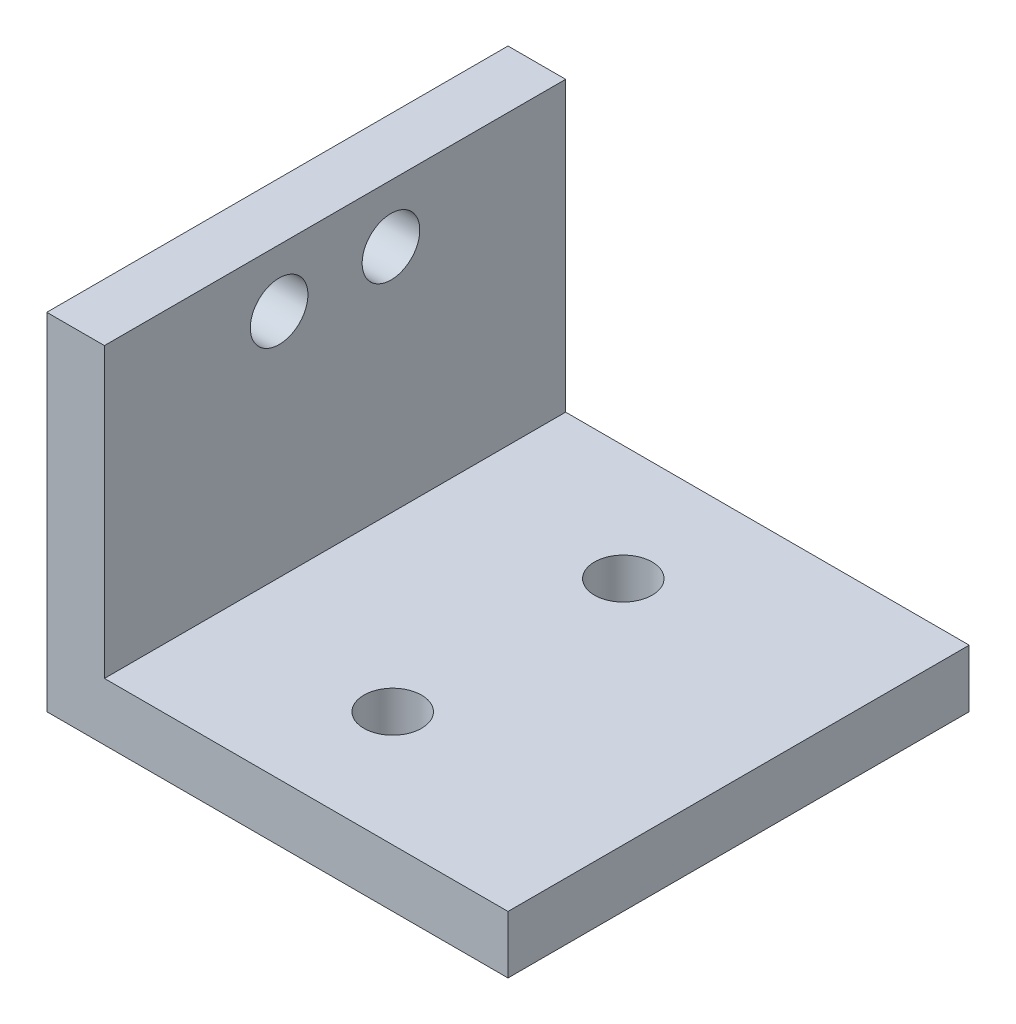
SolidWorks part; units mm, degrees
material "1060 Alloy"
ref_plane "Front Plane" through (0, 0, 0) normal (0, 0, 1) x (1, 0, 0)
ref_plane "Top Plane" through (0, 0, 0) normal (0, 1, 0) x (1, 0, 0)
ref_plane "Right Plane" through (0, 0, 0) normal (1, 0, 0) x (0, 0, -1)
sketch "Sketch1" plane through (0, 0, 0) normal (0, 0, 1) x (1, 0, 0)
  line L0 (0, 0) -> (0, 30)
  line L1 (0, 0) -> (40, 0)
  line L2 (5, 5) -> (40, 5)
  line L3 (5, 5) -> (5, 30)
  line L4 (5, 30) -> (0, 30)
  line L5 (40, 5) -> (40, 0)
  dimension "D1" = 5
extrude "Boss-Extrude1" add sketch "Sketch1" along normal blind 40
sketch "Sketch2" plane through (0, 0, 0) normal (-1, 0, 0) x (0, 0, 1)
  line L0 (40, 0) -> (0, 0) construction
  line L2 (40, 30) -> (40, 0) construction
  circle A0 centre (24.85, 25) radius 2.5
  circle A1 centre (15.15, 25) radius 2.5
  dimension "D1" = 9.7
  dimension "D2" = 25
  dimension "D3" = 15.15
extrude "Cut-Extrude1" cut sketch "Sketch2" against normal blind 40
sketch "Sketch3" plane through (0, 0, 0) normal (0, -1, 0) x (1, 0, 0)
  line L0 (0, 40) -> (40, 40) construction
  circle A0 centre (20, 30) radius 2.5
  circle A1 centre (20, 10) radius 2.5
  point P4 (20, 40)
  dimension "D1" = 20
  dimension "D2" = 10
extrude "Cut-Extrude2" cut sketch "Sketch3" against normal blind 40
